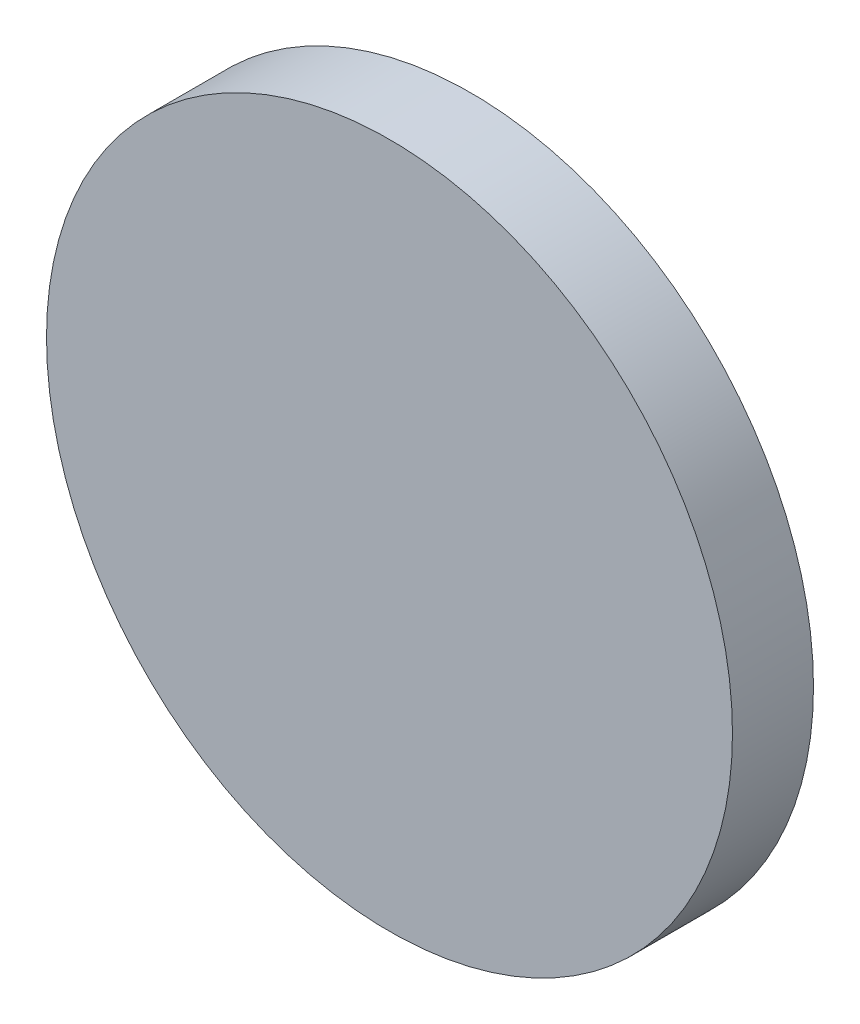
SolidWorks part; units mm, degrees
ref_plane "Front Plane" through (0, 0, 0) normal (0, 0, 1) x (1, 0, 0)
ref_plane "Top Plane" through (0, 0, 0) normal (0, 1, 0) x (1, 0, 0)
ref_plane "Right Plane" through (0, 0, 0) normal (1, 0, 0) x (0, 0, -1)
sketch "Sketch1" plane through (0, 0, 0) normal (0, 0, 1) x (1, 0, 0)
  circle A0 centre (0, 0) radius 12.7
extrude "Extrude1" add sketch "Sketch1" along normal blind 3
